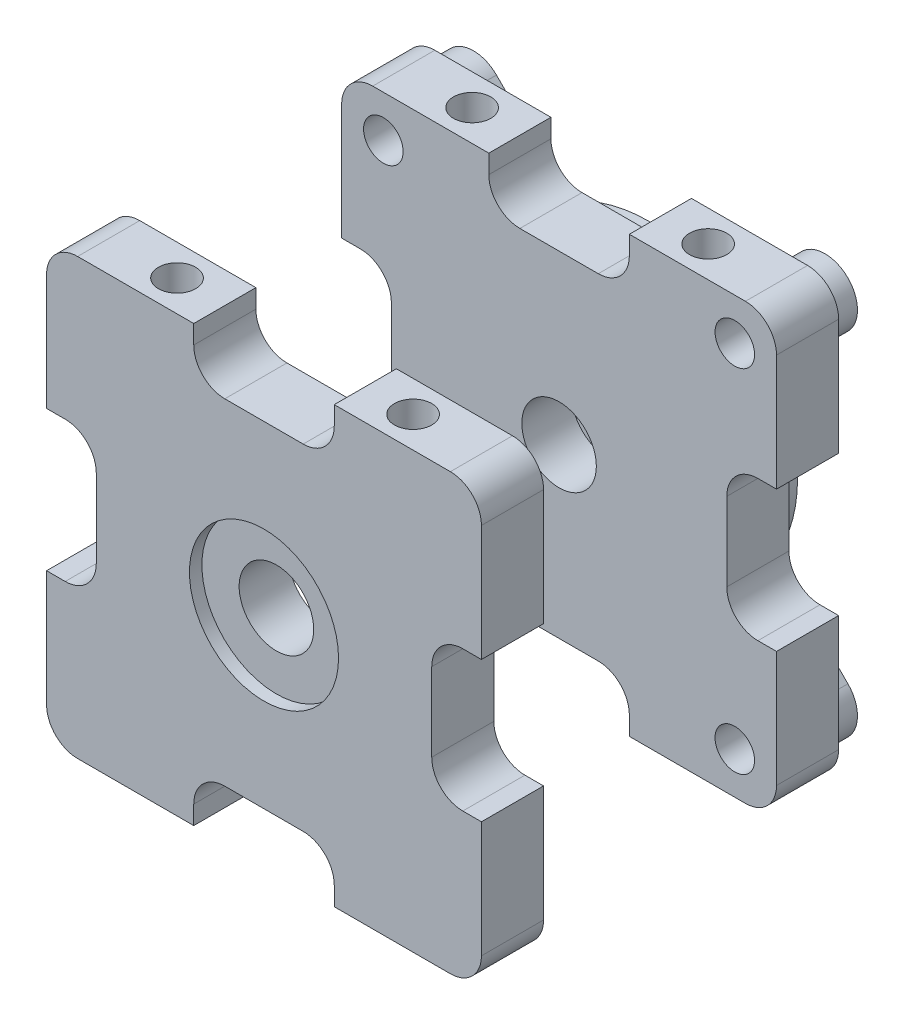
SolidWorks part; units mm, degrees
material "6063-T6"
ref_plane "Front Plane" through (0, 0, 0) normal (0, 0, 1) x (1, 0, 0)
ref_plane "Top Plane" through (0, 0, 0) normal (0, 1, 0) x (1, 0, 0)
ref_plane "Right Plane" through (0, 0, 0) normal (1, 0, 0) x (0, 0, -1)
sketch "Sketch1" plane through (0, 0, 0) normal (0, 0, 1) x (1, 0, 0)
  line L0 (-11.3088, 43) -> (-11.3088, 35) construction
  line L1 (-30, 35) -> (-11.3088, 35)
  line L2 (-35, 30) -> (-35, 11.3088)
  line L3 (-30, -35) -> (-11.31, -35)
  line L4 (35, 30) -> (35, 11.3106)
  line L5 (-35, 35) -> (35, -35) construction
  line L6 (-35, -35) -> (35, 35) construction
  line L7 (-11.3088, 43) -> (11.3088, 43) construction
  line L8 (-11.3088, 35) -> (-11.3088, 32)
  line L9 (-6.3088, 27) -> (6.3088, 27)
  line L10 (11.3088, 35) -> (11.3088, 32)
  line L11 (0, 35) -> (11.3088, 27) construction
  line L12 (-11.3088, 27) -> (0, 35) construction
  line L13 (-11.3088, 43) -> (0, 35) construction
  line L14 (0, 35) -> (11.3088, 43) construction
  line L15 (11.3088, 43) -> (11.3088, 35) construction
  line L16 (-11.3088, 35) -> (0, 35) construction
  line L17 (11.3088, 35) -> (30, 35)
  line L18 (0, 35) -> (11.3088, 35) construction
  line L19 (35, 11.3106) -> (32, 11.3106)
  line L20 (27, 6.3106) -> (27, -6.3106)
  line L21 (35, -11.3106) -> (32, -11.3106)
  line L22 (11.31, -35) -> (11.31, -32)
  line L23 (6.31, -27) -> (-6.31, -27)
  line L24 (-11.31, -35) -> (-11.31, -32)
  line L25 (-35, -11.3088) -> (-32, -11.3088)
  line L26 (-27, -6.3088) -> (-27, 6.3088)
  line L27 (-35, 11.3088) -> (-32, 11.3088)
  line L28 (-35, 11.3088) -> (-35, -11.3088) construction
  line L29 (-35, -11.3088) -> (-35, -30)
  line L30 (-11.31, -35) -> (11.31, -35) construction
  line L31 (11.31, -35) -> (30, -35)
  line L32 (35, 11.3106) -> (35, -11.3106) construction
  line L33 (35, -11.3106) -> (35, -30)
  line L34 (0, 35) -> (0, -35) construction
  line L35 (-35, 0) -> (35, 0) construction
  arc A1 (-35, -30) -> (-30, -35) centre (-30, -30) ccw
  arc A2 (30, -35) -> (35, -30) centre (30, -30) ccw
  arc A3 (35, 30) -> (30, 35) centre (30, 30) ccw
  arc A4 (-30, 35) -> (-35, 30) centre (-30, 30) ccw
  arc A5 (-6.31, -27) -> (-11.31, -32) centre (-6.31, -32) ccw
  arc A6 (11.31, -32) -> (6.31, -27) centre (6.31, -32) ccw
  arc A7 (27, -6.3106) -> (32, -11.3106) centre (32, -6.3106) ccw
  arc A8 (27, 6.3106) -> (32, 11.3106) centre (32, 6.3106) cw
  arc A9 (6.3088, 27) -> (11.3088, 32) centre (6.3088, 32) ccw
  arc A10 (-6.3088, 27) -> (-11.3088, 32) centre (-6.3088, 32) cw
  arc A11 (-32, -11.3088) -> (-27, -6.3088) centre (-32, -6.3088) ccw
  arc A12 (-27, 6.3088) -> (-32, 11.3088) centre (-32, 6.3088) ccw
  point P0 (0, 0)
  point P6 (0, -27)
  point P8 (0, 35)
  point P31 (0, 0)
  point P59 (0, 27)
  point P62 (-27, 0)
  dimension "D3" = 5
  dimension "D4" = 5
  dimension "D11" = 8
  dimension "D1" = 70
  dimension "D2" = 70
  dimension "D5" = 8
  dimension "D6" = 8
  dimension "D7" = 22.6177
  dimension "D8" = 22.6177
  dimension "D9" = 8
  dimension "D10" = 22.6212
  dimension "D12" = 22.62
extrude "Boss-Extrude1" add sketch "Sketch1" along normal blind 10
sketch "Sketch2" plane through (0, 35, 0) normal (0, 1, 0) x (1, 0, 0)
  line L0 (0, 0) -> (0, -10) construction
  line L1 (6.3088, -10) -> (-6.3088, -10) construction
  line L2 (-35, -5) -> (35, -5) construction
  line L3 (35, -10) -> (35, 0) construction
  circle A0 centre (-19, -5) radius 3
  circle A1 centre (19, -5) radius 3
  point P10 (0, -5)
  dimension "D1" = 6
  dimension "D2" = 38
extrude "Cut-Extrude1" cut sketch "Sketch2" against normal through all
sketch "Sketch3" plane through (0, 0, 10) normal (0, 0, 1) x (1, 0, 0)
  circle A0 centre (0, 0) radius 12
  dimension "D1" = 24
extrude "Cut-Extrude2" cut sketch "Sketch3" against normal blind 2
sketch "Sketch4" plane through (0, 0, 8) normal (0, 0, 1) x (1, 0, 0)
  circle A0 centre (0, 0) radius 6
extrude "Cut-Extrude3" cut sketch "Sketch4" against normal through all
ref_plane "Plane2" through (0, 0, -18.75) normal (0, 0, -1) x (-1, 0, 0)
mirror "Mirror12" about plane through (0, 0, -18.75) normal (0, 0, -1) of bodies 104
sketch "Sketch5" plane through (0, 0, -47.5) normal (0, 0, -1) x (-1, 0, 0)
  line L0 (-28.2879, 28.2879) -> (-16.4791, 16.4791) construction
  line L1 (-33.5355, 33.5355) -> (33.5355, 33.5355) construction
  line L2 (-33.5355, 33.5355) -> (-33.5355, -33.5355) construction
  line L3 (-33.5355, -33.5355) -> (33.5355, -33.5355) construction
  line L4 (33.5355, 33.5355) -> (33.5355, -33.5355) construction
  line L5 (-33.5355, 33.5355) -> (33.5355, -33.5355) construction
  line L6 (-33.5355, -33.5355) -> (33.5355, 33.5355) construction
  line L7 (-24.5773, 31.9986) -> (-15.3196, 22.7408)
  line L8 (-31.9986, 24.5773) -> (-22.7408, 15.3196)
  line L9 (24.5773, 31.9986) -> (15.3196, 22.7408)
  line L10 (31.9986, 24.5773) -> (22.7408, 15.3196)
  line L11 (28.2879, 28.2879) -> (16.4791, 16.4791) construction
  line L12 (31.9986, -24.5773) -> (22.7408, -15.3196)
  line L13 (24.5773, -31.9986) -> (15.3196, -22.7408)
  line L14 (28.2879, -28.2879) -> (16.4791, -16.4791) construction
  line L15 (-24.5773, -31.9986) -> (-15.3196, -22.7408)
  line L16 (-31.9986, -24.5773) -> (-22.7408, -15.3196)
  line L17 (-28.2879, -28.2879) -> (-16.4791, -16.4791) construction
  arc A0 (30, -35) -> (35, -30) centre (30, -30) ccw construction
  arc A1 (-24.5773, 31.9986) -> (-31.9986, 24.5773) centre (-28.2879, 28.2879) ccw
  arc A2 (-20.1897, 12.7685) -> (-12.7685, 12.7685) centre (-16.4791, 16.4791) ccw construction
  arc A3 (31.9986, 24.5773) -> (24.5773, 31.9986) centre (28.2879, 28.2879) ccw
  arc A4 (12.7685, 12.7685) -> (20.1897, 12.7685) centre (16.4791, 16.4791) ccw construction
  arc A5 (24.5773, -31.9986) -> (31.9986, -24.5773) centre (28.2879, -28.2879) ccw
  arc A6 (12.7685, -12.7685) -> (12.7685, -20.1897) centre (16.4791, -16.4791) ccw construction
  arc A7 (-31.9986, -24.5773) -> (-24.5773, -31.9986) centre (-28.2879, -28.2879) ccw
  arc A8 (-12.7685, -12.7685) -> (-20.1897, -12.7685) centre (-16.4791, -16.4791) ccw construction
  arc A9 (-21.7521, 9.8746) -> (-21.7521, -9.8746) centre (0, 0) ccw
  arc A10 (-12.7685, 12.7685) -> (-12.7685, 20.1897) centre (-16.4791, 16.4791) ccw construction
  arc A11 (12.7685, 20.1897) -> (12.7685, 12.7685) centre (16.4791, 16.4791) ccw construction
  arc A12 (20.1897, -12.7685) -> (12.7685, -12.7685) centre (16.4791, -16.4791) ccw construction
  arc A13 (-12.7685, -20.1897) -> (-12.7685, -12.7685) centre (-16.4791, -16.4791) ccw construction
  arc A14 (-16.8917, 16.8917) -> (-20.1897, 12.7685) centre (0, 0) ccw construction
  arc A15 (-12.7685, 20.1897) -> (-16.8917, 16.8917) centre (0, 0) ccw construction
  arc A16 (16.8917, 16.8917) -> (12.7685, 20.1897) centre (0, 0) ccw construction
  arc A17 (9.8746, 21.7521) -> (-9.8746, 21.7521) centre (0, 0) ccw
  arc A18 (20.1897, 12.7685) -> (16.8917, 16.8917) centre (0, 0) ccw construction
  arc A19 (16.8917, -16.8917) -> (20.1897, -12.7685) centre (0, 0) ccw construction
  arc A20 (21.7521, -9.8746) -> (21.7521, 9.8746) centre (0, 0) ccw
  arc A21 (12.7685, -20.1897) -> (16.8917, -16.8917) centre (0, 0) ccw construction
  arc A22 (-16.8917, -16.8917) -> (-12.7685, -20.1897) centre (0, 0) ccw construction
  arc A23 (-9.8746, -21.7521) -> (9.8746, -21.7521) centre (0, 0) ccw
  arc A24 (-20.1897, -12.7685) -> (-16.8917, -16.8917) centre (0, 0) ccw construction
  arc A25 (-21.7521, -9.8746) -> (-22.7408, -15.3196) centre (-26.177, -11.8833) cw
  arc A26 (-15.3196, -22.7408) -> (-9.8746, -21.7521) centre (-11.8833, -26.177) cw
  arc A27 (9.8746, -21.7521) -> (15.3196, -22.7408) centre (11.8833, -26.177) cw
  arc A28 (22.7408, -15.3196) -> (21.7521, -9.8746) centre (26.177, -11.8833) cw
  arc A29 (21.7521, 9.8746) -> (22.7408, 15.3196) centre (26.177, 11.8833) cw
  arc A30 (15.3196, 22.7408) -> (9.8746, 21.7521) centre (11.8833, 26.177) cw
  arc A31 (-9.8746, 21.7521) -> (-15.3196, 22.7408) centre (-11.8833, 26.177) cw
  arc A32 (-21.7521, 9.8746) -> (-22.7408, 15.3196) centre (-26.177, 11.8833) ccw
  point P0 (0, 0)
  point P11 (-22.3835, 22.3835)
  point P21 (22.3835, 22.3835)
  point P28 (22.3835, -22.3835)
  point P35 (-22.3835, -22.3835)
  point P40 (0, 0)
  dimension "D2" = 4.8596
  dimension "D1" = 4
extrude "Boss-Extrude2" add sketch "Sketch5" along normal blind 4.5
sketch "Sketch6" plane through (0, 0, -52) normal (0, 0, -1) x (-1, 0, 0)
  circle A0 centre (-28.2879, 28.2879) radius 3.182
  circle A1 centre (28.2879, 28.2879) radius 3.182
  circle A2 centre (28.2879, -28.2879) radius 3.182
  circle A3 centre (-28.2879, -28.2879) radius 3.182
  circle A4 centre (0, 0) radius 6
  point P12 (0, 0)
  dimension "D1" = 4
extrude "Cut-Extrude4" cut sketch "Sketch6" against normal up to next (14.5 mm away)
